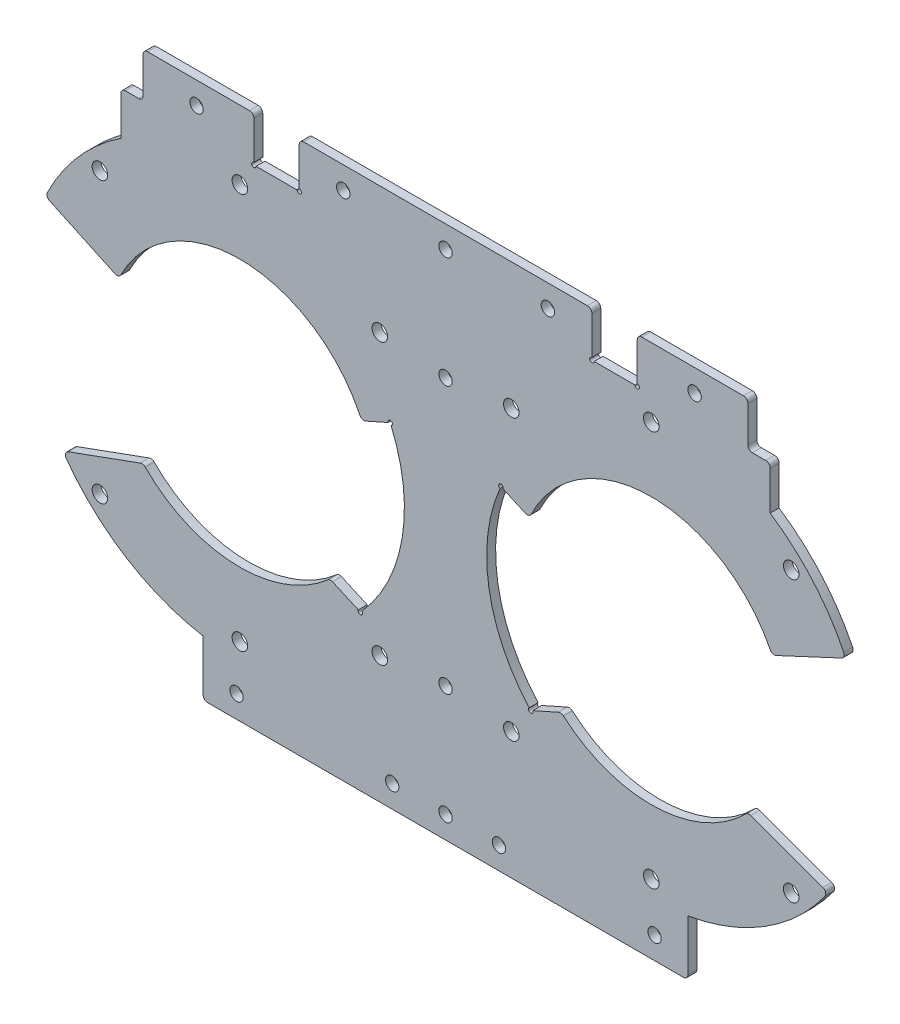
SolidWorks part; units mm, degrees
material "环氧板3240"
ref_plane "前视基准面" through (0, 0, 0) normal (0, 0, 1) x (1, 0, 0)
ref_plane "上视基准面" through (0, 0, 0) normal (0, 1, 0) x (1, 0, 0)
ref_plane "右视基准面" through (0, 0, 0) normal (1, 0, 0) x (0, 0, -1)
other "Configuration Table"
sketch "草图1" plane through (0, 0, 0) normal (0, 0, 1) x (1, 0, 0)
  line L0 (-46.25, 0) -> (-94.5, 0) construction
  line L5 (-54.5, -60) -> (-54.5, -47.5395)
  line L6 (-54.5, -55) -> (54.5, -55) construction
  line L7 (-46.25, 0) -> (46.25, 0) construction
  line L8 (-98.5273, -31.7975) -> (-79.7335, -24.9571) construction
  line L9 (0, 60) -> (0, -60) construction
  line L10 (54.5, -60) -> (54.5, -47.5395)
  line L11 (-46.25, 0) -> (-46.25, -44.5) construction
  line L12 (-46.25, 0) -> (-14.7837, -31.4663) construction
  line L14 (86.0613, -27.2603) -> (67.983, -20.6803)
  line L17 (46.25, 0) -> (14.7837, -31.4663) construction
  line L18 (46.25, 0) -> (46.25, -44.5) construction
  line L19 (46.25, 0) -> (86.0613, -27.2603) construction
  line L20 (46.25, 0) -> (94.5, 0) construction
  line L23 (-98.5273, -31.7975) -> (-102.6316, -20.5212) construction
  line L24 (-73, 55) -> (73, 55) construction
  line L27 (-79.7335, -24.9571) -> (-83.8377, -13.6808) construction
  line L28 (-54.5, -60) -> (54.5, -60)
  line L30 (-46.25, 0) -> (-102.6316, -20.5212) construction
  line L32 (-73.4392, 12.6785) -> (-46.25, 0) construction
  line L34 (-73, 60) -> (73, 60)
  line L35 (73, 60) -> (73, 40.1559)
  line L36 (-73, 60) -> (-73, 40.1559)
  line L37 (-73.4392, 12.6785) -> (-89.9794, 20.3913)
  line L38 (73.4392, 12.6785) -> (89.9794, 20.3913)
  line L39 (0, 13.7477) -> (0, -13.7477) construction
  line L45 (-86.0613, -27.2603) -> (-67.983, -20.6803)
  line L77 (-43.1, 60) -> (-43.1, 49.9)
  line L78 (-43.1, 49.9) -> (-32.9, 49.9)
  line L79 (-32.9, 49.9) -> (-32.9, 60)
  line L80 (32.9, 60) -> (32.9, 49.9)
  line L81 (32.9, 49.9) -> (43.1, 49.9)
  line L82 (43.1, 49.9) -> (43.1, 60)
  circle A0 centre (-46.25, 0) radius 30 construction
  circle A1 centre (-46.25, 0) radius 44.5 construction
  circle A2 centre (-14.7837, -31.4663) radius 1.75
  circle A3 centre (-77.7163, -31.4663) radius 1.75
  circle A4 centre (-46.25, -44.5) radius 1.75
  circle A6 centre (46.25, 0) radius 44.5 construction
  arc A7 (0, 13.7477) -> (0, -13.7477) centre (46.25, 0) cw construction
  circle A8 centre (46.25, -44.5) radius 1.75
  circle A9 centre (77.7163, -31.4663) radius 1.75
  circle A10 centre (14.7837, -31.4663) radius 1.75
  circle A11 centre (46.25, 0) radius 30 construction
  circle A12 centre (0, -30) radius 1.5
  circle A14 centre (0, -55) radius 1.5
  circle A16 centre (-47, -55) radius 1.5
  circle A17 centre (47, -55) radius 1.5
  circle A18 centre (-12, -55) radius 1.5
  circle A19 centre (12, -55) radius 1.5
  arc A21 (0, 13.7477) -> (0, -13.7477) centre (-46.25, 0) ccw construction
  arc A22 (-73, 40.1559) -> (-89.9794, 20.3913) centre (-46.25, 0) ccw
  arc A25 (89.9794, 20.3913) -> (73, 40.1559) centre (46.25, 0) ccw
  arc A26 (73.4392, 12.6785) -> (67.983, -20.6803) centre (46.25, 0) ccw
  arc A27 (54.5, -47.5395) -> (86.0613, -27.2603) centre (46.25, 0) ccw
  arc A28 (-73.4392, 12.6785) -> (-67.983, -20.6803) centre (-46.25, 0) cw
  arc A29 (-86.0613, -27.2603) -> (-54.5, -47.5395) centre (-46.25, 0) ccw
  circle A50 centre (0, 55) radius 1.5
  circle A51 centre (0, 30) radius 1.5
  circle A52 centre (-23, 55) radius 1.5
  circle A53 centre (23, 55) radius 1.5
  circle A54 centre (56, 55) radius 1.5
  circle A55 centre (-56, 55) radius 1.5
  circle A58 centre (77.7163, 31.4663) radius 1.75
  circle A59 centre (46.25, 44.5) radius 1.75
  circle A60 centre (14.7837, 31.4663) radius 1.75
  circle A61 centre (-14.7837, 31.4663) radius 1.75
  circle A62 centre (-46.25, 44.5) radius 1.75
  circle A63 centre (-77.7163, 31.4663) radius 1.75
  point P26 (0, 0)
  dimension "D2" = 60
  dimension "D4" = 3.5
  dimension "D5" = 89
  dimension "D14" = 3
  dimension "D16" = 24
  dimension "D9" = 5
  dimension "D11" = 7.5
  dimension "D20" = 48.25
  dimension "D21" = 60
  dimension "D28" = 40
  dimension "D47" = 46
  dimension "D49" = 112
  dimension "D6" = 94
  dimension "D26" = 20
  dimension "D15" = 30
  dimension "D3" = 45
  dimension "D7" = 92.5
  dimension "D8" = 12
  dimension "D10" = 60
  dimension "D12" = 25
  dimension "D13" = 20
  dimension "D22" = 146
  dimension "D23" = 5
  dimension "D44" = 10.2
  dimension "D45" = 65.8
  dimension "D46" = 10.1
extrude "凸台-拉伸1" add sketch "草图1" along normal blind 2
sketch "草图7" plane through (0, 0, 2) normal (0, 0, 1) x (1, 0, 0)
  line L0 (12.4488, 15.0493) -> (46.25, 0) construction
  line L2 (46.25, 0) -> (-46.25, 0) construction
  line L3 (46.25, 0) -> (12.4488, -15.0493) construction
  line L4 (19.1567, -25.1983) -> (26.0125, -22.146) construction
  line L5 (9.3951, 3.2732) -> (16.2508, 0.2209) construction
  line L6 (19.1567, -25.1983) -> (26.0125, -22.146)
  line L7 (12.4488, 15.0493) -> (18.8436, 12.2021)
  arc A3 (12.4488, 15.0493) -> (9.3951, 3.2732) centre (46.25, 0) ccw construction
  arc A4 (18.8436, 12.2021) -> (16.2508, 0.2209) centre (46.25, 0) ccw construction
  arc A5 (18.8436, -12.2021) -> (26.0125, -22.146) centre (46.25, 0) ccw construction
  arc A6 (12.4488, -15.0493) -> (19.1567, -25.1983) centre (46.25, 0) ccw construction
  arc A7 (73.4392, 12.6785) -> (67.983, -20.6803) centre (46.25, 0) ccw construction
  arc A8 (12.4488, 15.0493) -> (19.1567, -25.1983) centre (46.25, 0) ccw
  arc A9 (18.8436, 12.2021) -> (26.0125, -22.146) centre (46.25, 0) ccw
  arc A10 (-67.983, -20.6803) -> (-73.4392, 12.6785) centre (-46.25, 0) ccw construction
  dimension "D1" = 60
  dimension "D3" = 12
  dimension "D2" = 74
  dimension "D4" = 24
  dimension "D5" = 12
  dimension "D6" = 24
extrude "切除-拉伸3" cut sketch "草图7" against normal blind 10
mirror "镜向2" about plane through (0, 0, 0) normal (1, 0, 0) of "切除-拉伸3"
sketch "草图2" plane through (0, 0, 2) normal (0, 0, 1) x (1, 0, 0)
  line L2 (-43.1, 60) -> (-43.1, 49.9) construction
  line L3 (-43.1, 49.9) -> (-32.9, 49.9) construction
  circle A0 centre (-43.1, 49.9) radius 0.5
  circle A1 centre (-32.9, 49.9) radius 0.5
  circle A2 centre (32.9, 49.9) radius 0.5
  circle A3 centre (43.1, 49.9) radius 0.5
  circle A4 centre (-12.4488, 15.0493) radius 0.5
  circle A5 centre (12.4488, 15.0493) radius 0.5
  circle A6 centre (-19.1567, -25.1983) radius 0.5
  circle A7 centre (19.1567, -25.1983) radius 0.5
  dimension "D1" = 1
extrude "切除-拉伸1" cut sketch "草图2" against normal blind 10
sketch "草图8" plane through (0, 0, 0) normal (0, 0, -1) x (-1, 0, 0)
  line L0 (0, 60) -> (0, 0) construction
  line L1 (68, 49.9) -> (73, 49.9)
  line L2 (68, 49.9) -> (68, 60)
  line L3 (68, 60) -> (73, 60)
  line L4 (73, 49.9) -> (73, 60)
  line L6 (32.9, 60) -> (-32.9, 60) construction
  line L7 (42.6, 49.9) -> (33.4, 49.9) construction
  line L8 (-68, 60) -> (-73, 60)
  line L9 (-73, 49.9) -> (-73, 60)
  line L10 (-68, 49.9) -> (-73, 49.9)
  line L11 (-68, 49.9) -> (-68, 60)
  dimension "D1" = 5
extrude "切除-拉伸4" cut sketch "草图8" against normal blind 10
fillet "圆角2" radius 1 24 edges at (54.5, -60, 1) (89.9794, 20.3913, 1) (86.0613, -27.2603, 1) (67.983, -20.6803, 1) (43.1, 60, 1) (32.9, 60, 1) (-43.1, 60, 1) (-32.9, 60, 1) (-89.9794, 20.3913, 1) (-67.983, -20.6803, 1) (-86.0613, -27.2603, 1) (-54.5, -60, 1) (73.4392, 12.6785, 1) (18.8436, 12.2021, 1) (-18.8436, 12.2021, 1) (26.0125, -22.146, 1) (-26.0125, -22.146, 1) (-73.4392, 12.6785, 1) (68, 49.9, 1) (73, 49.9, 1) (68, 60, 1) (-68, 49.9, 1) (-68, 60, 1) (-73, 49.9, 1)
